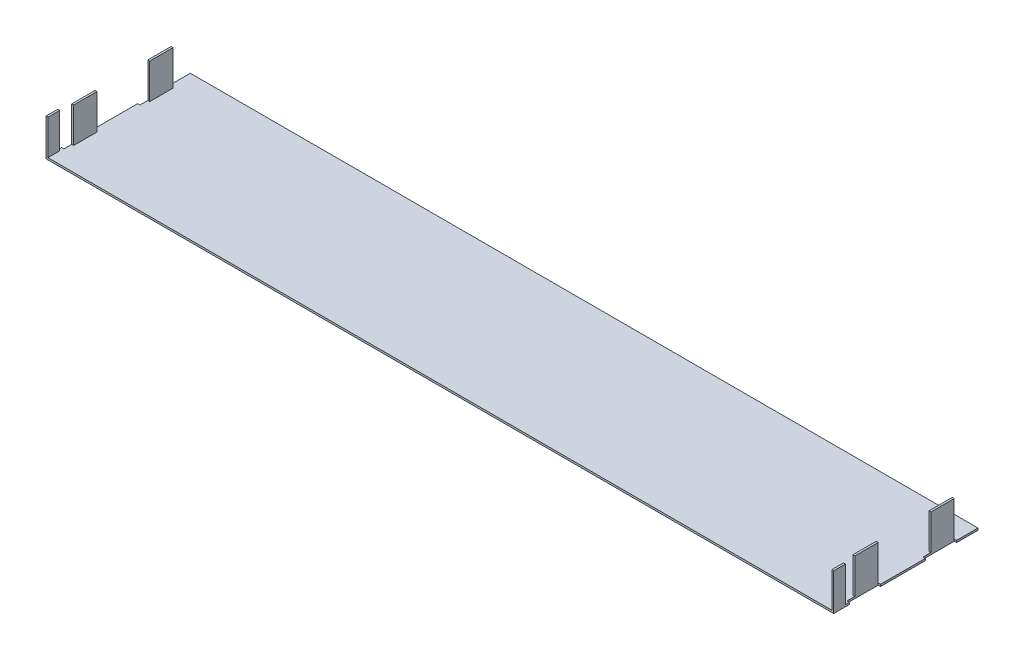
SolidWorks part; units mm, degrees
ref_plane "Front Plane" through (0, 0, 0) normal (0, 0, 1) x (1, 0, 0)
ref_plane "Top Plane" through (0, 0, 0) normal (0, 1, 0) x (1, 0, 0)
ref_plane "Right Plane" through (0, 0, 0) normal (1, 0, 0) x (0, 0, -1)
sketch "Sketch1" plane through (0, 0, 0) normal (0, 1, 0) x (1, 0, 0)
  line L1 (0, 0) -> (101, 0)
  line L2 (0, 0) -> (0, 37)
  line L3 (0, 37) -> (101, 37)
  line L4 (101, 0) -> (101, 37)
  dimension "D1" = 37
  dimension "D2" = 101
extrude "Boss-MainBridgeRightHalf" add sketch "Sketch1" along normal blind 0.5
sketch "Sketch2" plane through (0, 0.5, 0) normal (0, 1, 0) x (1, 0, 0)
  line L0 (101, 0) -> (101, 37) construction
  line L1 (101, 3) -> (100.5, 3)
  line L2 (101, 3) -> (101, 0)
  line L3 (101, 0) -> (100.5, 0)
  line L4 (100.5, 3) -> (100.5, 0)
  line L5 (0, 0) -> (101, 0) construction
  line L6 (101, 37) -> (0, 37) construction
  line L7 (100.4, 31.5) -> (99.9, 31.5)
  line L8 (100.4, 31.5) -> (100.4, 25.5)
  line L9 (100.4, 25.5) -> (99.9, 25.5)
  line L10 (99.9, 31.5) -> (99.9, 25.5)
  line L11 (100.4, 12) -> (99.9, 12)
  line L12 (100.4, 12) -> (100.4, 6)
  line L13 (100.4, 6) -> (99.9, 6)
  line L14 (99.9, 12) -> (99.9, 6)
  dimension "D1" = 0.6
  dimension "D2" = 0.6
  dimension "D3" = 6
  dimension "D4" = 6
  dimension "D5" = 3
  dimension "D6" = 0.5
  dimension "D7" = 0.5
  dimension "D8" = 0.5
  dimension "D9" = 5.5
  dimension "D10" = 13.5
extrude "Boss-MetalTabs" add sketch "Sketch2" along normal blind 9
sketch "Sketch3" plane through (0, 0.5, 0) normal (0, 1, 0) x (1, 0, 0)
  line L0 (101, 3) -> (101, 37) construction
  line L1 (100.4, 31.5) -> (101, 31.5)
  line L2 (100.4, 31.5) -> (100.4, 23.5)
  line L3 (100.4, 23.5) -> (101, 23.5)
  line L4 (101, 31.5) -> (101, 23.5)
  line L6 (100.4, 12) -> (101, 12)
  line L7 (100.4, 12) -> (100.4, 4)
  line L8 (100.4, 4) -> (101, 4)
  line L9 (101, 12) -> (101, 4)
  dimension "D1" = 8
  dimension "D2" = 8
extrude "Cut-Extrude1" cut sketch "Sketch3" against normal through all
mirror "Mirror1" about plane through (0, 0.5, 0) normal (1, 0, 0) of "Boss-MainBridgeRightHalf", "Boss-MetalTabs", "Cut-Extrude1"
